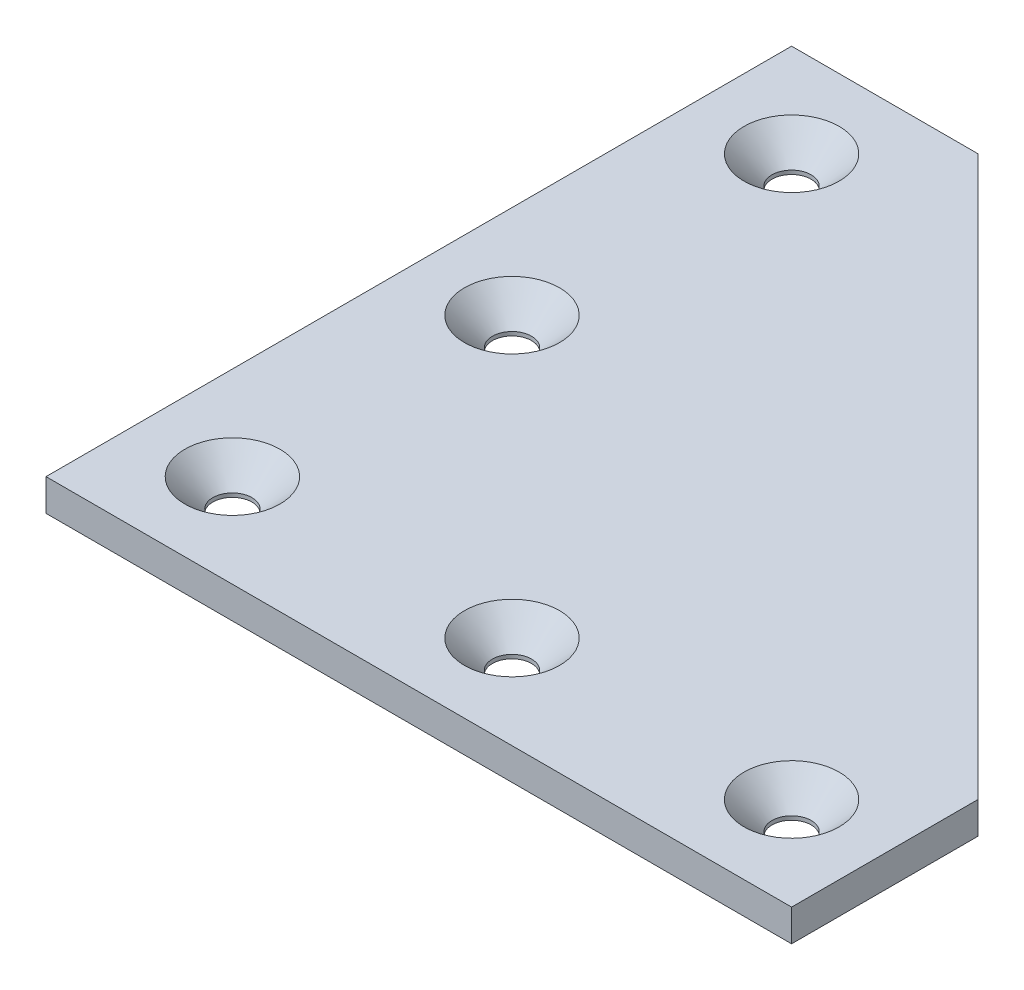
SolidWorks part; units mm, degrees
material "AISI 1010 Steel, hot rolled bar"
ref_plane "Front Plane" through (0, 0, 0) normal (0, 0, 1) x (1, 0, 0)
ref_plane "Top Plane" through (0, 0, 0) normal (0, 1, 0) x (1, 0, 0)
ref_plane "Right Plane" through (0, 0, 0) normal (1, 0, 0) x (0, 0, -1)
sketch "Sketch1" plane through (0, 0, 0) normal (0, 1, 0) x (1, 0, 0)
  line L0 (0, 0) -> (0, 80)
  line L1 (0, 80) -> (20, 80)
  line L2 (20, 80) -> (80, 20)
  line L3 (80, 20) -> (80, 0)
  line L4 (80, 0) -> (0, 0)
  dimension "D1" = 20
  dimension "D2" = 20
  dimension "D3" = 45
  dimension "D4" = 80
extrude "Boss-Extrude1" add sketch "Sketch1" along normal blind 3.416
fillet "Fillet1" [suppressed] radius 1
sketch "Sketch3" plane through (0, 3.416, 0) normal (0, 1, 0) x (1, 0, 0)
  line L0 (0, 80) -> (0, 0) construction
  line L1 (0, 0) -> (80, 0) construction
  line L3 (80, 0) -> (80, 20) construction
  line L4 (20, 80) -> (0, 80) construction
  circle A2 centre (10, 10) radius 2.1
  circle A5 centre (40, 10) radius 2.1
  circle A6 centre (70, 10) radius 2.1
  circle A7 centre (10, 40) radius 2.1
  circle A8 centre (10, 70) radius 2.1
  dimension "D3" = 4.2
  dimension "D7" = 10
  dimension "D1" = 10
  dimension "D2" = 10
  dimension "D4" = 3
  dimension "D6" = 10
  dimension "D5" = 3
extrude "Cut-Extrude1" cut sketch "Sketch3" against normal blind 4
chamfer "Chamfer1" distance 3 angle 45 5 edges at (70, 3.416, -7.9) (40, 3.416, -7.9) (10, 3.416, -7.9) (10, 3.416, -37.9) (10, 3.416, -67.9)
